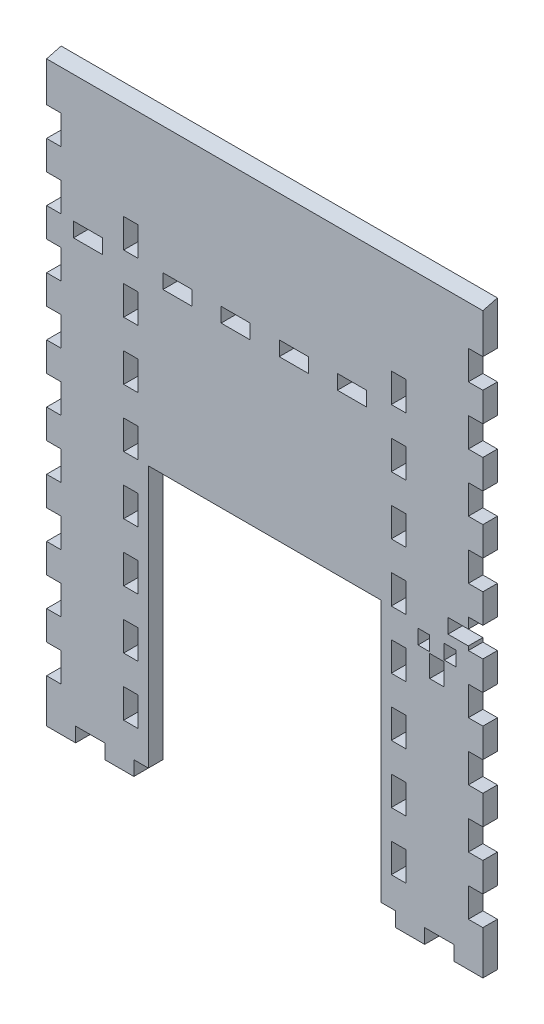
SolidWorks part; units mm, degrees
material "Balsa"
ref_plane "Alzado" through (0, 0, 0) normal (0, 0, 1) x (1, 0, 0)
ref_plane "Planta" through (0, 0, 0) normal (0, 1, 0) x (1, 0, 0)
ref_plane "Vista lateral" through (0, 0, 0) normal (1, 0, 0) x (0, 0, -1)
sketch "Croquis1" plane through (0, 0, 0) normal (0, 0, 1) x (1, 0, 0)
  line L0 (10, 0) -> (10, 5)
  line L1 (0, 0) -> (150, 0)
  line L2 (0, 0) -> (0, 200)
  line L3 (0, 200) -> (150, 200)
  line L4 (150, 0) -> (150, 200)
  line L5 (35, 0) -> (115, 0)
  line L6 (35, 0) -> (35, 95)
  line L7 (35, 95) -> (115, 95)
  line L8 (115, 0) -> (115, 95)
  line L9 (10, 5) -> (20, 5)
  line L10 (20, 5) -> (20, 0)
  line L11 (30, 0) -> (30, 5)
  line L12 (30, 5) -> (35, 5)
  line L13 (115, 5) -> (115, 0)
  line L14 (40, 155) -> (40, 150)
  line L19 (40, 155) -> (50, 155)
  line L20 (40, 150) -> (50, 150)
  line L21 (50, 155) -> (50, 150)
  line L22 (60, 155) -> (60, 150)
  line L23 (60, 155) -> (70, 155)
  line L29 (150, 15) -> (145, 15)
  line L30 (145, 15) -> (145, 25)
  line L31 (145, 25) -> (150, 25)
  line L32 (145, 45) -> (150, 45)
  line L33 (145, 35) -> (145, 45)
  line L34 (150, 35) -> (145, 35)
  line L35 (145, 65) -> (150, 65)
  line L36 (145, 55) -> (145, 65)
  line L37 (150, 55) -> (145, 55)
  line L38 (145, 85) -> (150, 85)
  line L39 (145, 75) -> (145, 85)
  line L40 (150, 75) -> (145, 75)
  line L41 (145, 105) -> (150, 105)
  line L42 (145, 95) -> (145, 105)
  line L43 (150, 95) -> (145, 95)
  line L44 (145, 125) -> (150, 125)
  line L45 (145, 115) -> (145, 125)
  line L46 (150, 115) -> (145, 115)
  line L47 (145, 145) -> (150, 145)
  line L48 (145, 135) -> (145, 145)
  line L49 (150, 135) -> (145, 135)
  line L50 (145, 165) -> (150, 165)
  line L51 (145, 155) -> (145, 165)
  line L52 (150, 155) -> (145, 155)
  line L53 (145, 185) -> (150, 185)
  line L54 (145, 175) -> (145, 185)
  line L55 (150, 175) -> (145, 175)
  line L56 (60, 150) -> (70, 150)
  line L57 (0, 175) -> (5, 175)
  line L58 (5, 175) -> (5, 185)
  line L59 (5, 185) -> (0, 185)
  line L60 (0, 155) -> (5, 155)
  line L61 (5, 155) -> (5, 165)
  line L62 (5, 165) -> (0, 165)
  line L63 (0, 135) -> (5, 135)
  line L64 (5, 135) -> (5, 145)
  line L65 (5, 145) -> (0, 145)
  line L66 (0, 115) -> (5, 115)
  line L67 (5, 115) -> (5, 125)
  line L68 (5, 125) -> (0, 125)
  line L69 (0, 95) -> (5, 95)
  line L70 (5, 95) -> (5, 105)
  line L71 (5, 105) -> (0, 105)
  line L72 (0, 75) -> (5, 75)
  line L73 (5, 75) -> (5, 85)
  line L74 (5, 85) -> (0, 85)
  line L75 (0, 55) -> (5, 55)
  line L76 (5, 55) -> (5, 65)
  line L77 (5, 65) -> (0, 65)
  line L78 (0, 35) -> (5, 35)
  line L79 (5, 35) -> (5, 45)
  line L80 (5, 45) -> (0, 45)
  line L81 (5, 25) -> (0, 25)
  line L82 (5, 15) -> (5, 25)
  line L83 (0, 15) -> (5, 15)
  line L84 (50, 5) -> (60, 5) [skipped]
  line L85 (50, 0) -> (50, 5) [skipped]
  line L86 (60, 5) -> (60, 0) [skipped]
  line L87 (70, 0) -> (70, 5) [skipped]
  line L88 (70, 5) -> (80, 5) [skipped]
  line L89 (80, 5) -> (80, 0) [skipped]
  line L90 (90, 0) -> (90, 5) [skipped]
  line L91 (90, 5) -> (100, 5) [skipped]
  line L92 (100, 5) -> (100, 0) [skipped]
  line L93 (40, 5) -> (40, 0) [skipped]
  line L94 (110, 0) -> (110, 5) [skipped]
  line L95 (70, 155) -> (70, 150)
  line L96 (80, 155) -> (80, 150)
  line L97 (80, 155) -> (90, 155)
  line L98 (80, 150) -> (90, 150)
  line L99 (90, 155) -> (90, 150)
  line L100 (100, 155) -> (100, 150)
  line L101 (100, 155) -> (110, 155)
  line L102 (100, 150) -> (110, 150)
  line L103 (110, 155) -> (110, 150)
  line L108 (0, 25) -> (0, 15)
  line L109 (0, 45) -> (0, 35)
  line L110 (0, 65) -> (0, 55)
  line L111 (0, 85) -> (0, 75)
  line L112 (0, 105) -> (0, 95)
  line L113 (0, 125) -> (0, 115)
  line L114 (0, 145) -> (0, 135)
  line L115 (0, 165) -> (0, 155)
  line L116 (0, 185) -> (0, 175)
  line L117 (150, 185) -> (150, 175)
  line L118 (150, 165) -> (150, 155)
  line L119 (150, 145) -> (150, 135)
  line L120 (150, 125) -> (150, 115)
  line L121 (150, 105) -> (150, 95)
  line L122 (150, 85) -> (150, 75)
  line L123 (150, 65) -> (150, 55)
  line L124 (150, 45) -> (150, 35)
  line L125 (150, 25) -> (150, 15)
  line L127 (112.5, 0) -> (115, 0)
  line L128 (115, 5) -> (115, 0)
  line L129 (10, 0) -> (20, 0)
  line L130 (30, 0) -> (35, 0)
  line L131 (35, 5) -> (35, 0)
  line L132 (123.5001, 15) -> (118.5001, 15)
  line L133 (26.5, 25) -> (31.5, 25)
  line L134 (26.5, 25) -> (26.5, 15)
  line L135 (26.5, 15) -> (31.5, 15)
  line L136 (31.5, 25) -> (31.5, 15)
  line L137 (9.25, 155) -> (19.25, 155)
  line L138 (9.25, 155) -> (9.25, 150)
  line L139 (9.25, 150) -> (19.25, 150)
  line L140 (19.25, 155) -> (19.25, 150)
  line L145 (140, 5) -> (140, 0) [skipped]
  line L146 (130, 5) -> (140, 5) [skipped]
  line L147 (130, 0) -> (130, 5) [skipped]
  line L148 (115, 5) -> (117.5, 5) [skipped]
  line L149 (120, 5) -> (120, 0) [skipped]
  line L150 (115, 5) -> (115, 0)
  line L151 (120, 5) -> (115, 5)
  line L152 (120, 0) -> (120, 5)
  line L153 (120, 0) -> (115, 0)
  line L154 (140, 0) -> (140, 5)
  line L155 (140, 5) -> (130, 5)
  line L156 (130, 5) -> (130, 0)
  line L157 (140, 0) -> (130, 0)
  line L158 (120, 0) -> (115, 0)
  line L159 (26.5, 45) -> (26.5, 35)
  line L160 (26.5, 35) -> (31.5, 35)
  line L161 (31.5, 45) -> (31.5, 35)
  line L162 (26.5, 45) -> (31.5, 45)
  line L163 (26.5, 65) -> (26.5, 55)
  line L164 (26.5, 55) -> (31.5, 55)
  line L165 (31.5, 65) -> (31.5, 55)
  line L166 (26.5, 65) -> (31.5, 65)
  line L167 (26.5, 85) -> (26.5, 75)
  line L168 (26.5, 75) -> (31.5, 75)
  line L169 (31.5, 85) -> (31.5, 75)
  line L170 (26.5, 85) -> (31.5, 85)
  line L171 (26.5, 105) -> (26.5, 95)
  line L172 (26.5, 95) -> (31.5, 95)
  line L173 (31.5, 105) -> (31.5, 95)
  line L174 (26.5, 105) -> (31.5, 105)
  line L175 (26.5, 125) -> (26.5, 115)
  line L176 (26.5, 115) -> (31.5, 115)
  line L177 (31.5, 125) -> (31.5, 115)
  line L178 (26.5, 125) -> (31.5, 125)
  line L179 (26.5, 145) -> (26.5, 135)
  line L180 (26.5, 135) -> (31.5, 135)
  line L181 (31.5, 145) -> (31.5, 135)
  line L182 (26.5, 145) -> (31.5, 145)
  line L183 (31.5, -11.0421) -> (31.5, 132.4455) construction
  line L184 (118.5001, 25) -> (118.5001, 15)
  line L185 (123.5001, 25) -> (118.5001, 25)
  line L186 (123.5001, 25) -> (123.5001, 15)
  line L187 (123.5001, 45) -> (118.5001, 45)
  line L188 (118.5001, 45) -> (118.5001, 35)
  line L189 (123.5001, 35) -> (118.5001, 35)
  line L190 (123.5001, 45) -> (123.5001, 35)
  line L191 (123.5005, 65) -> (118.5005, 65)
  line L192 (118.5005, 65) -> (118.5005, 55)
  line L193 (123.5005, 55) -> (118.5005, 55)
  line L194 (123.5005, 65) -> (123.5005, 55)
  line L195 (123.5001, 85) -> (118.5001, 85)
  line L196 (118.5001, 85) -> (118.5001, 75)
  line L197 (123.5001, 75) -> (118.5001, 75)
  line L198 (123.5001, 85) -> (123.5001, 75)
  line L199 (123.5001, 105) -> (118.5001, 105)
  line L200 (118.5001, 105) -> (118.5001, 95)
  line L201 (123.5001, 95) -> (118.5001, 95)
  line L202 (123.5001, 105) -> (123.5001, 95)
  line L203 (123.5001, 125) -> (118.5001, 125)
  line L204 (118.5001, 125) -> (118.5001, 115)
  line L205 (123.5001, 115) -> (118.5001, 115)
  line L206 (123.5001, 125) -> (123.5001, 115)
  line L207 (123.5001, 145) -> (118.5001, 145)
  line L208 (118.5001, 145) -> (118.5001, 135)
  line L209 (123.5001, 135) -> (118.5001, 135)
  line L210 (123.5001, 145) -> (123.5001, 135)
  line L211 (118.5, -7.0008) -> (118.5, 146.9996) construction
  line L212 (26.5, 165) -> (26.5, 155)
  line L213 (26.5, 155) -> (31.5, 155)
  line L214 (31.5, 165) -> (31.5, 155)
  line L215 (26.5, 165) -> (31.5, 165)
  line L216 (123.5001, 165) -> (118.5001, 165)
  line L217 (118.5001, 165) -> (118.5001, 155)
  line L218 (123.5001, 155) -> (118.5001, 155)
  line L219 (123.5001, 165) -> (123.5001, 155)
  dimension "D1" = 150
  dimension "D2" = 200
  dimension "D3" = 80
  dimension "D4" = 95
  dimension "D5" = 35
  dimension "D6" = 5
  dimension "D7" = 10
  dimension "D8" = 10
  dimension "D10" = 5
  dimension "D11" = 10
  dimension "D12" = 15
  dimension "D14" = 3.5
  dimension "D15" = 5
  dimension "D16" = 10
  dimension "D17" = 9.25
  dimension "D19" = 5
  dimension "D20" = 0.0001
  dimension "D21" = 10
  dimension "D22" = 15
  dimension "D23" = 3.5
  dimension "D27" = 0.001
  dimension "D28" = 5
  dimension "D29" = 0.0001
  dimension "D30" = 0.0001
  dimension "D31" = 0.0001
  dimension "D32" = 0.0001
  dimension "D33" = 0.0001
  dimension "D34" = 0.0001
  dimension "D36" = 10
  dimension "D37" = 10
  dimension "D38" = 10
  dimension "D39" = 10
  dimension "D40" = 15
  dimension "D9" = 7
  dimension "D13" = 9
  dimension "D26" = 7
  dimension "D41" = 2
  dimension "D42" = 2
extrude "Saliente-Extruir1" add sketch "Croquis1" along normal blind 5 contours L156 L155 L154 L1 L4 L29 L30 L31 L34 L33 L32 L37 L36 L35 L40 L39 L38 L43 L42 L41 L46 L45 L44 L49 L48 L47 L52 L51 L50 L55 L54 L53 L3 L2 L59 L58 L57 L62 L61 L60
sketch "Croquis7" plane through (0, 0, 0) normal (-1, 0, 0) x (0, 0, 1)
  line L0 (0, 200) -> (5.3174, 198.6007)
  line L1 (5, 200) -> (0, 200) construction
  line L2 (0, 200) -> (5, 200)
  line L4 (5, 185) -> (5, 200) construction
  line L5 (5, 200) -> (5.3174, 198.6007)
  dimension "D1" = 14.744
extrude "Cortar-Extruir7" cut sketch "Croquis7" against normal through all
sketch "Croquis8" plane through (0, 0, 5) normal (0, 0, 1) x (1, 0, 0)
  line L0 (123.5001, 85) -> (123.5001, 75) construction
  line L1 (127.7001, 93) -> (131.7001, 93)
  line L2 (127.7001, 93) -> (127.7001, 88)
  line L3 (127.7001, 88) -> (131.7001, 88)
  line L4 (131.7001, 93) -> (131.7001, 88)
  line L5 (131.7001, 87.5) -> (136.7001, 87.5)
  line L6 (131.7001, 87.5) -> (131.7001, 80)
  line L7 (131.7001, 80) -> (136.7001, 80)
  line L8 (136.7001, 87.5) -> (136.7001, 80)
  line L9 (136.7001, 93) -> (140.7001, 93)
  line L10 (136.7001, 93) -> (136.7001, 88)
  line L11 (136.7001, 88) -> (140.7001, 88)
  line L12 (140.7001, 93) -> (140.7001, 88)
  line L13 (120, 0) -> (130, 0) construction
  line L14 (125.7752, 98.875) -> (142.3547, 98.875) construction
  line L17 (138, 101.375) -> (145, 101.375)
  line L18 (138, 101.375) -> (138, 96.375)
  line L19 (138, 96.375) -> (145, 96.375)
  line L20 (145, 101.375) -> (145, 96.375)
  line L21 (145, 95) -> (145, 105) construction
  dimension "D1" = 0.5
  dimension "D2" = 5
  dimension "D3" = 7.5
  dimension "D4" = 5
  dimension "D5" = 4
  dimension "D6" = 5
  dimension "D7" = 4
  dimension "D8" = 0
  dimension "D9" = 0
  dimension "D10" = 0.5
  dimension "D11" = 88
  dimension "D12" = 4.2
  dimension "D13" = 5.875
  dimension "D14" = 7
  dimension "D15" = 5
  dimension "D16" = 2.5
extrude "Cortar-Extruir12" cut sketch "Croquis8" against normal blind 10
